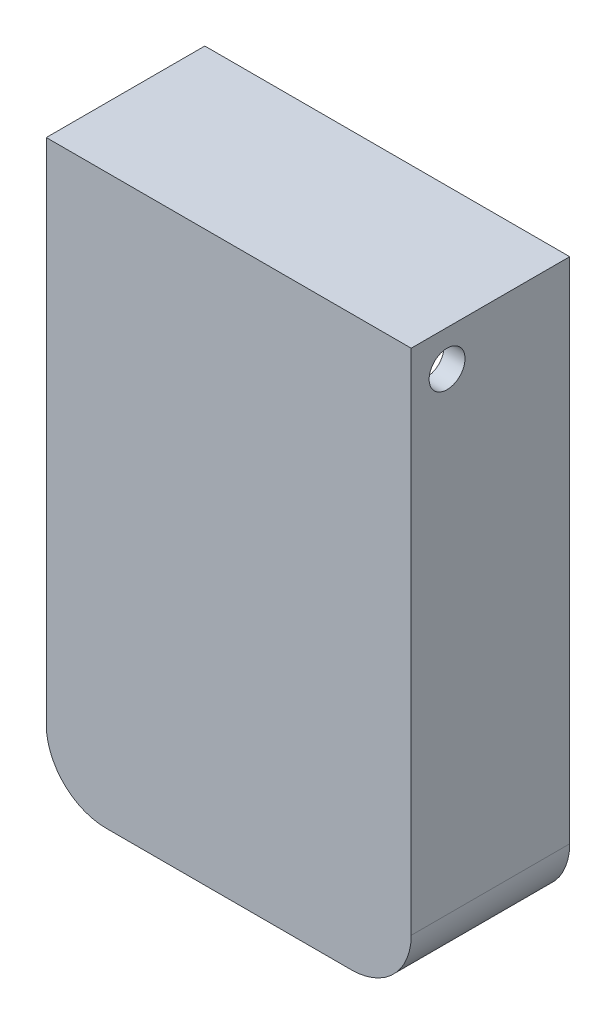
SolidWorks part; units mm, degrees
ref_plane "Front Plane" through (0, 0, 0) normal (0, 0, 1) x (1, 0, 0)
ref_plane "Top Plane" through (0, 0, 0) normal (0, 1, 0) x (1, 0, 0)
ref_plane "Right Plane" through (0, 0, 0) normal (1, 0, 0) x (0, 0, -1)
sketch "Sketch1" plane through (0, 0, 0) normal (0, 0, 1) x (1, 0, 0)
  line L1 (-30.5, 47.5) -> (30.5, 47.5)
  line L2 (-30.5, 47.5) -> (-30.5, -47.5)
  line L3 (-30.5, -47.5) -> (30.5, -47.5)
  line L4 (30.5, 47.5) -> (30.5, -47.5)
  line L5 (-30.5, 47.5) -> (30.5, -47.5) construction
  line L6 (-30.5, -47.5) -> (30.5, 47.5) construction
  point P0 (0, 0)
  dimension "D1" = 61
  dimension "D2" = 95
extrude "Boss-Extrude1" add sketch "Sketch1" along normal blind 25
shell "Shell1" thickness 1.5
fillet "Fillet1" radius 10 4 edges at (29, -46, 11.75) (-29, -46, 11.75) (-30.5, -47.5, 12.5) (30.5, -47.5, 12.5)
sketch "Sketch2" plane through (0, 0, 23.5) normal (0, 0, -1) x (-1, 0, 0)
  circle A0 centre (-21.5, 12) radius 3
  circle A1 centre (-21.5, 12) radius 1.4
  circle A2 centre (-21.5, -31) radius 3
  circle A3 centre (-21.5, -31) radius 1.4
  circle A4 centre (21.5, -31) radius 3
  circle A5 centre (21.5, -31) radius 1.4
  point P4 (0, 0)
  dimension "D1" = 6
  dimension "D3" = 2.8
  dimension "D2" = 21.5
  dimension "D6" = 12
  dimension "D4" = 2
  dimension "D5" = 2
extrude "Boss-Extrude2" add sketch "Sketch2" along normal blind 4
sketch "Sketch4" plane through (0, 0, 23.5) normal (0, 0, -1) x (-1, 0, 0)
  line L0 (-30.5, -37.5) -> (-30.5, 47.5) construction
  line L1 (-29, 46) -> (-27, 46)
  line L2 (-29, 46) -> (-29, 28)
  line L3 (-29, 28) -> (-27, 28)
  line L4 (-27, 46) -> (-27, 28)
  line L5 (0, 35.2777) -> (0, -7.0736) construction
  line L6 (27, 46) -> (27, 28)
  line L7 (29, 28) -> (27, 28)
  line L8 (29, 46) -> (29, 28)
  line L9 (29, 46) -> (27, 46)
  dimension "D1" = 3.5
  dimension "D2" = 18
extrude "Boss-Extrude3" add sketch "Sketch4" along normal up to surface (23.5 mm away) up to face at (0, -12.6904, 0)
sketch "Sketch3" plane through (30.5, 0, 0) normal (1, 0, 0) x (0, 0, -1)
  line L0 (-25, 47.5) -> (0, 47.5) construction
  line L1 (-25, -37.5) -> (-25, 47.5) construction
  circle A0 centre (-19, 41.5) radius 3
  dimension "D1" = 6
  dimension "D2" = 6
  dimension "D3" = 6
extrude "Cut-Extrude1" cut sketch "Sketch3" against normal through all both and the other way through all
sketch "Sketch5" plane through (0, 0, 0) normal (0, 0, -1) x (-1, 0, 0)
  line L0 (-30.5, 47.5) -> (30.5, 47.5)
  line L1 (-30.5, 47.5) -> (30.5, 47.5) construction
  line L2 (30.5, 47.5) -> (30.5, -37.5)
  line L3 (-20.5, -47.5) -> (20.5, -47.5)
  line L4 (20.5, -47.5) -> (-20.5, -47.5) construction
  line L5 (-19.75, -46.75) -> (19.75, -46.75)
  line L6 (29.75, -36.75) -> (29.75, 46.75)
  line L7 (29.75, 46.75) -> (-29.75, 46.75)
  line L8 (0, 4.0791) -> (0, -5.3806) construction
  line L9 (-29.75, -36.75) -> (-29.75, 46.75)
  line L10 (-30.5, 47.5) -> (-30.5, -37.5)
  arc A0 (20.5, -47.5) -> (30.5, -37.5) centre (20.5, -37.5) ccw
  arc A1 (19.75, -46.75) -> (29.75, -36.75) centre (19.75, -36.75) ccw
  arc A2 (-19.75, -46.75) -> (-29.75, -36.75) centre (-19.75, -36.75) cw
  arc A3 (-20.5, -47.5) -> (-30.5, -37.5) centre (-20.5, -37.5) cw
  point P6 (0, -47.5)
  point P14 (0, -46.75)
  point P21 (0, 0)
  point P22 (0, -46.75)
  point P30 (0, 46.75)
  point P31 (0, 47.5)
  dimension "D4" = 10
  dimension "D1" = 0.75
  dimension "D2" = 0.75
  dimension "D3" = 0.75
extrude "Boss-Extrude4" add sketch "Sketch5" along normal blind 1.5
sketch "Sketch6" plane through (0, 0, 0) normal (0, 0, -1) x (-1, 0, 0)
  line L0 (29.75, -36.75) -> (29.75, 46.75) construction
  line L1 (-29.75, 46.75) -> (29.75, 46.75)
  line L2 (-29.75, 46.75) -> (-29.75, 42.5)
  line L3 (-29.75, 42.5) -> (29.75, 42.5)
  line L4 (29.75, 46.75) -> (29.75, 42.5)
  dimension "D1" = 78.5
extrude "Boss-Extrude5" add sketch "Sketch6" along normal up to surface (1.5 mm away) up to face at (0, -13.1904, -1.5)
sketch "Sketch7" plane through (0, 0, 0) normal (0, 0, 1) x (1, 0, 0)
  line L0 (27, 42.5) -> (-27, 42.5) construction
  line L1 (26, 42.5) -> (-26, 42.5)
  line L2 (26, 42.5) -> (26, 43.5)
  line L3 (26, 43.5) -> (-26, 43.5)
  line L4 (-26, 42.5) -> (-26, 43.5)
  line L5 (-27, 28) -> (-27, 42.5) construction
  line L6 (27, 42.5) -> (27, 28) construction
  point P6 (0, 0)
  dimension "D1" = 1
  dimension "D2" = 1
  dimension "D3" = 1
extrude "Boss-Extrude6" add sketch "Sketch7" along normal blind 1
fillet "Fillet2" radius 0.3 2 edges at (0, 43.5, 1) (0, 42.5, 1)
sketch "Sketch8" plane through (0, 0, 23.5) normal (0, 0, -1) x (-1, 0, 0)
  line L0 (-22.5, -36.5) -> (-28.9875, -36.5)
  line L1 (-28.9875, -36.5) -> (-28.9875, -39)
  line L3 (-21.9875, -46) -> (-19.5, -46)
  line L4 (-19.5, -46) -> (-19.5, -39.5)
  line L5 (-29, -36) -> (-29, 28) construction
  line L6 (19, -46) -> (-19, -46) construction
  line L7 (0, -29.2192) -> (0, -41.085) construction
  line L8 (19.5, -46) -> (19.5, -39.5)
  line L9 (21.9875, -46) -> (19.5, -46)
  line L10 (28.9875, -36.5) -> (28.9875, -39)
  line L11 (22.5, -36.5) -> (28.9875, -36.5)
  arc A0 (-29, -36) -> (-19, -46) centre (-19, -36) ccw construction
  arc A1 (-22.5, -36.5) -> (-19.5, -39.5) centre (-22.5, -39.5) cw
  arc A2 (-28.9875, -39) -> (-21.9875, -46) centre (-21.9875, -39) ccw
  arc A3 (28.9875, -39) -> (21.9875, -46) centre (21.9875, -39) cw
  arc A4 (22.5, -36.5) -> (19.5, -39.5) centre (22.5, -39.5) ccw
  dimension "D3" = 3
  dimension "D5" = 7
  dimension "D1" = 9.5
  dimension "D2" = 9.5
  dimension "D4" = 0
extrude "Boss-Extrude7" add sketch "Sketch8" along normal offset from surface (19.5 mm away) 4 up to face at (0, -3.5803, 0)
sketch "Sketch9" plane through (0, 0, 4) normal (0, 0, -1) x (-1, 0, 0)
  line L0 (0, -23.162) -> (0, -54.7922) construction
  line L1 (-19.75, -46.75) -> (19.75, -46.75) construction
  line L2 (-19.5, -45.9875) -> (-19.5, -39.5) construction
  line L4 (-28.9875, -36.5) -> (-22.5, -36.5) construction
  circle A0 centre (-23, -40) radius 1.4
  circle A1 centre (23, -40) radius 1.4
  dimension "D1" = 23
  dimension "D3" = 2.8
  dimension "D2" = 6.75
  dimension "D4" = 3.5
  dimension "D5" = 3.5
extrude "Cut-Extrude2" cut sketch "Sketch9" against normal blind 10
